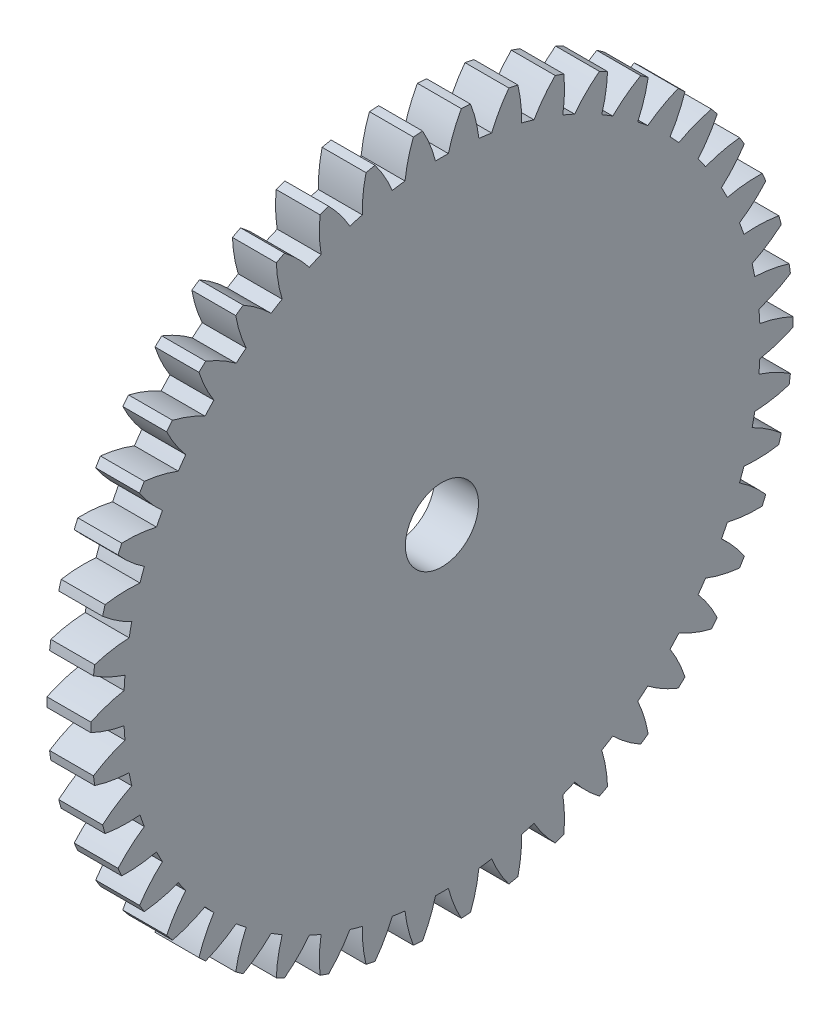
SolidWorks part; units mm, degrees
ref_plane "Plane1" through (0, 0, 0) normal (0, 0, 1) x (1, 0, 0)
ref_plane "Plane2" through (0, 0, 0) normal (0, 1, 0) x (1, 0, 0)
ref_plane "Plane3" through (0, 0, 0) normal (1, 0, 0) x (0, 0, -1)
sketch "HoldingSke" plane through (0, 0, 0) normal (0, 1, 0) x (1, 0, 0)
  line L0 (0, 0) -> (0.6947, -0.7193)
  line L1 (-15, 0) -> (100, 0) construction
  line L2 (0, 0) -> (-2.1039, 2.3779)
  line L3 (0, 0) -> (-11.863, 4.5341)
  line L4 (0, 0) -> (5.9991, 6.2122)
  line L5 (0, 0) -> (-46.8476, -17.4728)
  line L6 (0, 0) -> (-2.4869, -1.6779)
  line L7 (-2.1039, 2.3779) -> (8.6586, 51.2059)
  line L8 (-76.2, 54.61) -> (-75.3, 54.61)
  line L9 (-71.009, 38.7566) -> (-53.1078, 45.2721)
  line L10 (-76.2, 71.12) -> (104.1128, 71.12)
  line L11 (0, 0) -> (-3, 0)
  line L12 (-76.2, 101.6) -> (-76.162, 101.6)
  line L13 (24.9733, 27.94) -> (52.9518, 28.4284)
  line L14 (24.9733, 27.94) -> (24.9743, 27.94)
  line L15 (24.9733, 27.94) -> (100.4006, 29.5858)
  line L16 (-63.627, -1) -> (-12.827, -1)
  circle A0 centre (0, 0) radius 2.5
  circle A1 centre (0, 0) radius 21.749
  circle A2 centre (0, 0) radius 37.5
  circle A3 centre (0, 0) radius 2.5
  dimension "MHD" = 43.498
  dimension "Hub_dia" = 75
  dimension "Bore" = 5
  dimension "MBD" = 5
  dimension "Num_teeth" = 46
  dimension "Pitch_radius" = 180.3128
  dimension "Pitch" = 1
  dimension "Width" = 3
  dimension "Overall_len" = 50
  dimension "Show_teeth" = 46
  dimension "Thickness" = 3
  dimension "OAL" = 50.0001
  dimension "T_dim" = 0.9
  dimension "Ap" = 20
  dimension "H" = 19.05
  dimension "Backlash" = 0.038
  dimension "Addendum_fac" = 1
  dimension "Dedendum_fac" = 1.25
  dimension "Clearance_fac" = 0.25
  dimension "Dedendum_add" = 0.001
  dimension "Module" = 1
sketch "BasProSke" plane through (0, 0, 0) normal (0, 1, 0) x (1, 0, 0)
  line L0 (-10, 0) -> (60, 0) construction
  line L1 (0, 0) -> (0, 24)
  line L2 (0, 0) -> (3, 0)
  line L3 (3, 0) -> (3, 24)
  line L4 (3, 24) -> (0, 24)
  dimension "Diameter" = 48
  dimension "Thickness" = 3
revolve "Base-Revolve" add sketch "BasProSke" angle 360 about L0
sketch "TooCutSke" plane through (0, 0, 0) normal (1, 0, 0) x (0, 0, -1)
  line L1 (0, 0) -> (0, 107) construction
  line L2 (0, 0) -> (-0.8517, 22.9842) construction
  line L3 (0, 0) -> (-3.1376, 45.8703) construction
  line L4 (-0.8517, 22.9842) -> (-1.5688, 22.9352) construction
  arc A0 (0.4415, 21.7445) -> (-0.4415, 21.7445) centre (0, 0) ccw
  arc A1 (1.3382, 23.9881) -> (-1.3382, 23.9881) centre (0, 0) ccw
  circle A2 centre (0, 0) radius 23 construction
  circle A3 centre (0, 0) radius 21.6129 construction
  arc A4 (-0.4415, 21.7445) -> (-1.3382, 23.9881) centre (-9.3589, 19.4815) ccw
  arc A5 (1.3382, 23.9881) -> (0.4415, 21.7445) centre (9.3589, 19.4815) ccw
  dimension "Root_dia" = 43.498
  dimension "Overcut_dia" = 48.0508
  dimension "Pitch_dia" = 46
  dimension "Base_dia" = 43.2259
  dimension "Flank_rad" = 9.2
  dimension "Half_ang" = 3.913
  dimension "Half_CT" = 0.7187
extrude "ToothCut" cut sketch "TooCutSke" along normal through all
fillet "Breaks" [suppressed] radius 0.02
fillet "RootFillets" [suppressed] radius 0.251
pattern_circular "TeethCuts" count 46 every 7.826 about axis through (-10, 0, 0) along (1, 0, 0) of "ToothCut", "RootFillets", "Breaks"
sketch "HubNeaOneSke" plane through (0, 0, 0) normal (-1, 0, 0) x (0, 0, 1)
  circle A0 centre (0, 0) radius 21.749
  dimension "Diameter" = 43.498
extrude "HubNearOne" [suppressed] add sketch "HubNeaOneSke" along normal blind 47.0001
sketch "HubNeaBotSke" plane through (0, 0, 0) normal (-1, 0, 0) x (0, 0, 1)
  circle A0 centre (0, 0) radius 21.749
  dimension "Diameter" = 43.498
extrude "HubNearBoth" [suppressed] add sketch "HubNeaBotSke" along normal blind 23.5
ref_plane "FarPln" through (3, 0, 0) normal (1, 0, 0) x (0, 0, -1)
sketch "HubFarSke" plane through (3, 0, 0) normal (1, 0, 0) x (0, 0, -1)
  circle A0 centre (0, 0) radius 21.749
  dimension "Diameter" = 43.498
extrude "HubFar" [suppressed] add sketch "HubFarSke" along normal blind 23.5
sketch "BorSke" plane through (0, 0, 0) normal (1, 0, 0) x (0, 0, -1)
  circle A0 centre (0, 0) radius 2.5
  dimension "Diameter" = 5
extrude "Bore" cut sketch "BorSke" along normal mid plane 100.0001
sketch "KeySke" plane through (0, 0, 0) normal (1, 0, 0) x (0, 0, -1)
  line L0 (-1, 0) -> (-1, 3.4)
  line L1 (-1, 3.4) -> (1, 3.4)
  line L2 (1, 3.4) -> (1, 0)
  line L3 (0, 0) -> (0, 34) construction
  line L4 (-1, 0) -> (1, 0)
  dimension "Offset" = 3.4
  dimension "Width" = 2
extrude "Keyway" [suppressed] cut sketch "KeySke" along normal mid plane 100.0001
pattern_circular "Keyway2" [suppressed] count 2 every 90 about axis through (-10, 0, 0) along (1, 0, 0)
equation "' \"Module@HoldingSke\" = 6.35"
equation "' \"Num_teeth@HoldingSke\" = 12"
equation "' \"Ap@HoldingSke\" =  20"
equation "' \"Width@HoldingSke\" = 0.5 * 25.4"
equation "' \"Hub_dia@HoldingSke\"= 1 * 25.4"
equation "' \"Overall_len@HoldingSke\" = 1.0 * 25.4"
equation "' \"Bore@HoldingSke\" = 0.75 * 25.4"
equation "' \"T_dim@HoldingSke\" = 0.1 * 25.4"
equation "' \"Width@KeySke\" = 0.25 * 25.4"
equation "' \"Show_teeth@HoldingSke\" = 13"
equation "' \"Backlash@HoldingSke\" = 0.009 * 25.4"
equation "' \"Addendum_fac@HoldingSke\" = 1.0"
equation "' \"Dedendum_fac@HoldingSke\" = 1.25"
equation "' \"Dedendum_add@HoldingSke\" = 0.00005 * 25.4"
equation "' \"Clearance_fac@HoldingSke\" = 0.25"
equation "\"Pitch@HoldingSke\" = 1 / \"Module@HoldingSke\""
equation "\"Overcut_dia@TooCutSke\" = (\"Num_teeth@HoldingSke\" + 2 * \"Addendum_fac@HoldingSke\") / \"Pitch@HoldingSke\" + 0.002 * 25.4"
equation "\"Pitch_dia@TooCutSke\" = \"Num_teeth@HoldingSke\" / \"Pitch@HoldingSke\""
equation "\"Base_dia@TooCutSke\" = \"Num_teeth@HoldingSke\" / \"Pitch@HoldingSke\" * cos((\"Ap@HoldingSke\"  * 3.14159265 / 180))"
equation "\"Root_dia@TooCutSke\" = (\"Num_teeth@HoldingSke\" + 2) / \"Pitch@HoldingSke\" - 2 * (\"Addendum_fac@HoldingSke\" + \"Dedendum_fac@HoldingSke\") / \"Pitch@HoldingSke\" - \"Dedendum_add@HoldingSke\" * 2"
equation "\"Half_ang@TooCutSke\" = 180 / \"Num_teeth@HoldingSke\""
equation "\"Half_CT@TooCutSke\" = \"Num_teeth@HoldingSke\" / \"Pitch@HoldingSke\" * sin((3.14159265 / 2 / \"Num_teeth@HoldingSke\")) / 2 - 7 * \"Backlash@HoldingSke\" / 4"
equation "\"Flank_rad@TooCutSke\" = \"Num_teeth@HoldingSke\" / \"Pitch@HoldingSke\" / 5"
equation "\"Radius@RootFillets\" = \"Clearance_fac@HoldingSke\" / \"Pitch@HoldingSke\" + \"Dedendum_add@HoldingSke\""
equation "\"Break_rad@Breaks\" = 0.02 / \"Pitch@HoldingSke\""
equation "\"Thickness@HoldingSke\" = \"Width@HoldingSke\""
equation "\"OAL@HoldingSke\" = \"Thickness@HoldingSke\""
equation "\"MHD@HoldingSke\" = (\"Num_teeth@HoldingSke\" + 2) / \"Pitch@HoldingSke\" - 2 * (\"Addendum_fac@HoldingSke\" + \"Dedendum_fac@HoldingSke\")  / \"Pitch@HoldingSke\" - \"Dedendum_add@HoldingSke\" * 2"
equation "\"MBD@HoldingSke\" = (\"Num_teeth@HoldingSke\" + 2) / \"Pitch@HoldingSke\" - 2 * (\"Addendum_fac@HoldingSke\" + \"Dedendum_fac@HoldingSke\")  / \"Pitch@HoldingSke\" - \"Dedendum_add@HoldingSke\" * 2 - 0.002 * 25.4"
equation "\"MHD@HoldingSke\" = ((sgn( \"MHD@HoldingSke\" - \"Hub_dia@HoldingSke\" )-1)*( \"MHD@HoldingSke\" - \"Hub_dia@HoldingSke\" ))/-2+ \"Hub_dia@HoldingSke\""
equation "\"MBD@HoldingSke\" = ((sgn( \"MBD@HoldingSke\" - \"Bore@HoldingSke\" )-1)*( \"MBD@HoldingSke\" - \"Bore@HoldingSke\" ))/-2+ \"Bore@HoldingSke\""
equation "\"OAL@HoldingSke\" = ((sgn( \"OAL@HoldingSke\" - \"Overall_len@HoldingSke\" )+1)*( \"OAL@HoldingSke\" - \"Overall_len@HoldingSke\" ))/2 + \"Overall_len@HoldingSke\" + 0.000002 * 25.4"
equation "\"Num_teeth@TeethCuts\" = int( \"Show_teeth@HoldingSke\" ) + 1"
equation "\"Num_teeth@TeethCuts\" = ((sgn( \"Num_teeth@TeethCuts\" - \"Num_teeth@HoldingSke\" )-1)*( \"Num_teeth@TeethCuts\" - \"Num_teeth@HoldingSke\" ))/-2+ \"Num_teeth@HoldingSke\""
equation "\"Num_teeth@TeethCuts\" = ((sgn( \"Num_teeth@TeethCuts\" - 2.0)+1)*( \"Num_teeth@TeethCuts\" - 2.0))/2 +2.0"
equation "\"Angle@TeethCuts\" = 360.0 / \"Num_teeth@HoldingSke\""
equation "\"Diameter@BasProSke\" = (\"Num_teeth@HoldingSke\" + 2 * \"Addendum_fac@HoldingSke\") / \"Pitch@HoldingSke\""
equation "\"Thickness@BasProSke\"  = \"Thickness@HoldingSke\""
equation "' \"Fillet_rad@BasProSke\" =  \"Thickness@HoldingSke\" * 0.05"
equation "\"MHD@HoldingSke\" = ((sgn( \"MHD@HoldingSke\" - \"Root_dia@TooCutSke\" )-1)*( \"MHD@HoldingSke\" - \"Root_dia@TooCutSke\" ))/-2+ \"Root_dia@TooCutSke\""
equation "\"Diameter@HubNeaOneSke\" = \"MHD@HoldingSke\""
equation "\"Length@HubNearOne\" = \"OAL@HoldingSke\" - \"Thickness@BasProSke\""
equation "\"Diameter@HubNeaBotSke\" = \"MHD@HoldingSke\""
equation "\"Length@HubNearBoth\" = ( \"OAL@HoldingSke\" - \"Thickness@BasProSke\" ) / 2.0"
equation "\"Thickness@FarPln\" = \"Thickness@BasProSke\""
equation "\"Diameter@HubFarSke\" = \"MHD@HoldingSke\""
equation "\"Length@HubFar\" = ( \"OAL@HoldingSke\" - \"Thickness@BasProSke\" ) / 2.0"
equation "\"Diameter@BorSke\" = \"MBD@HoldingSke\""
equation "\"D1@Bore\" = \"OAL@HoldingSke\" * 2.0"
equation "\"D1@Keyway\" = \"OAL@HoldingSke\" * 2.0"
equation "\"Offset@KeySke\" = \"T_dim@HoldingSke\" + \"MBD@HoldingSke\" / 2.0"
